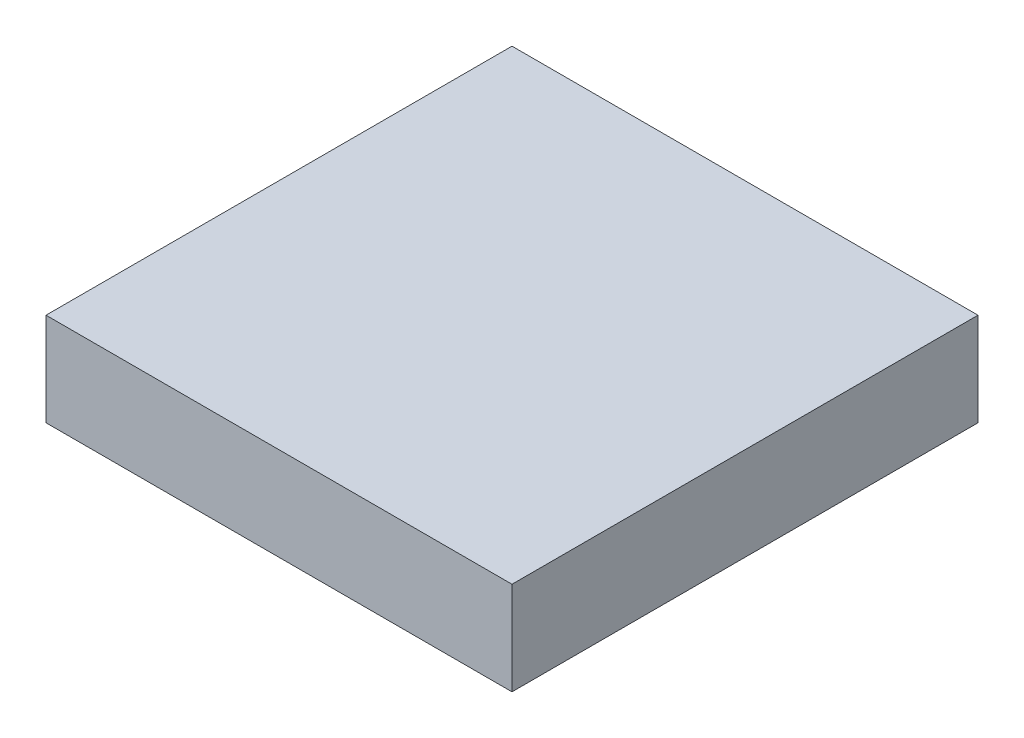
SolidWorks part; units mm, degrees
material "Литая легированная сталь"
ref_plane "Спереди" through (0, 0, 0) normal (0, 0, 1) x (1, 0, 0)
ref_plane "Сверху" through (0, 0, 0) normal (0, 1, 0) x (1, 0, 0)
ref_plane "Справа" through (0, 0, 0) normal (1, 0, 0) x (0, 0, -1)
sketch "Эскиз1" plane through (0, 0, 0) normal (0, 1, 0) x (1, 0, 0)
  line L1 (-1.75, -1.75) -> (1.75, -1.75)
  line L2 (-1.75, -1.75) -> (-1.75, 1.75)
  line L3 (-1.75, 1.75) -> (1.75, 1.75)
  line L4 (1.75, -1.75) -> (1.75, 1.75)
  line L5 (-1.75, -1.75) -> (1.75, 1.75) construction
  line L6 (-1.75, 1.75) -> (1.75, -1.75) construction
  point P0 (0, 0)
  dimension "D1" = 3.5
  dimension "D2" = 3.5
extrude "Бобышка-Вытянуть1" add sketch "Эскиз1" along normal blind 0.7
